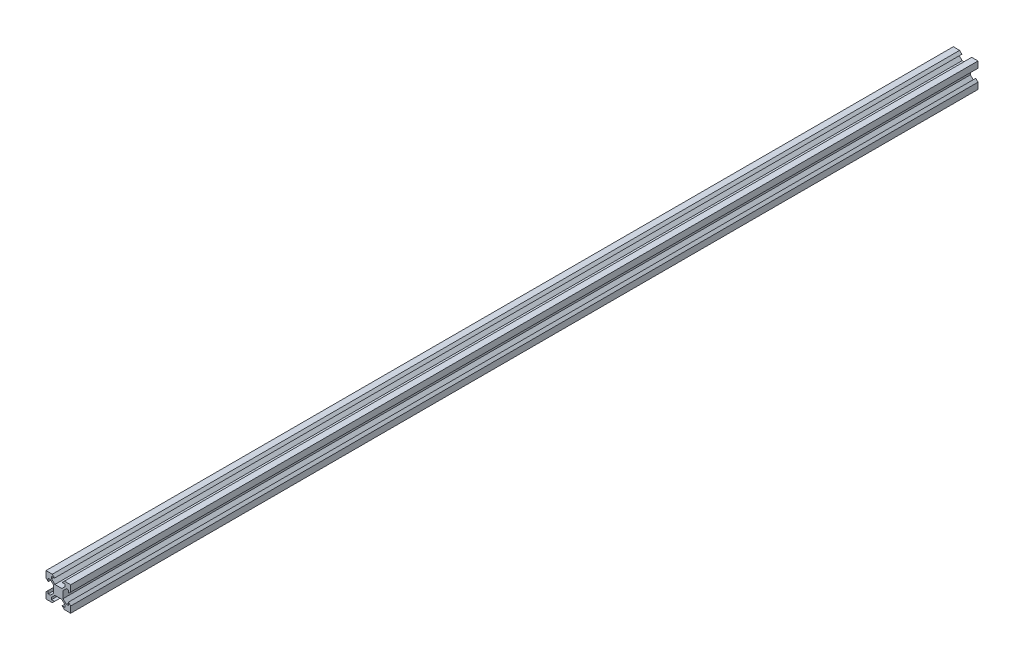
SolidWorks part; units mm, degrees
ref_plane "Front Plane" through (0, 0, 0) normal (0, 0, 1) x (1, 0, 0)
ref_plane "Top Plane" through (0, 0, 0) normal (0, 1, 0) x (1, 0, 0)
ref_plane "Right Plane" through (0, 0, 0) normal (1, 0, 0) x (0, 0, -1)
sketch "Sketch1" plane through (0, 0, 0) normal (0, 0, 1) x (1, 0, 0)
  line L1 (0, 0) -> (20, 0)
  line L2 (0, 0) -> (0, 20)
  line L3 (0, 20) -> (20, 20)
  line L4 (20, 0) -> (20, 20)
  line L5 (0, 0) -> (20, 20) construction
  line L6 (0, 20) -> (20, 0) construction
  point P4 (10, 10)
  dimension "D1" = 20
  dimension "D2" = 20
extrude "Boss-Extrude1" add sketch "Sketch1" along normal blind 735.01
sketch "Sketch2" plane through (0, 0, 735.01) normal (0, 0, 1) x (1, 0, 0)
  line L4 (0, 0) -> (20, 20) construction
  line L5 (4.5, 18.18) -> (6.94, 18.18)
  line L6 (4.5, 16.4758) -> (4.5, 18.18)
  line L15 (7.1658, 13.81) -> (4.5, 16.4758)
  line L17 (12.8342, 13.81) -> (7.1658, 13.81)
  line L27 (15.5, 16.4758) -> (12.8342, 13.81)
  line L29 (15.5, 18.18) -> (15.5, 16.4758)
  line L31 (13.06, 18.18) -> (15.5, 18.18)
  line L33 (14.88, 20) -> (5.12, 20)
  line L35 (6.94, 18.18) -> (5.12, 20)
  line L54 (14.88, 20) -> (13.06, 18.18)
  line L56 (14.88, 0) -> (13.06, 1.82)
  line L57 (6.94, 1.82) -> (5.12, 0)
  line L58 (14.88, 0) -> (5.12, 0)
  line L68 (13.06, 1.82) -> (15.5, 1.82)
  line L71 (15.5, 1.82) -> (15.5, 3.5242)
  line L81 (15.5, 3.5242) -> (12.8342, 6.19)
  line L82 (12.8342, 6.19) -> (7.1658, 6.19)
  line L83 (7.1658, 6.19) -> (4.5, 3.5242)
  line L84 (4.5, 3.5242) -> (4.5, 1.82)
  line L85 (4.5, 1.82) -> (6.94, 1.82)
  line L136 (20, 0) -> (10, 0) construction
  line L137 (0, 0) -> (20, 0) construction
  line L186 (1.82, 4.5) -> (1.82, 6.94)
  line L187 (3.5242, 4.5) -> (1.82, 4.5)
  line L188 (6.19, 7.1658) -> (3.5242, 4.5)
  line L189 (6.19, 12.8342) -> (6.19, 7.1658)
  line L190 (3.5242, 15.5) -> (6.19, 12.8342)
  line L191 (1.82, 15.5) -> (3.5242, 15.5)
  line L192 (1.82, 13.06) -> (1.82, 15.5)
  line L193 (0, 14.88) -> (0, 5.12)
  line L194 (1.82, 6.94) -> (0, 5.12)
  line L195 (0, 14.88) -> (1.82, 13.06)
  line L203 (20, 14.88) -> (18.18, 13.06)
  line L205 (18.18, 6.94) -> (20, 5.12)
  line L206 (20, 14.88) -> (20, 5.12)
  line L207 (18.18, 13.06) -> (18.18, 15.5)
  line L208 (18.18, 15.5) -> (16.4758, 15.5)
  line L209 (16.4758, 15.5) -> (13.81, 12.8342)
  line L210 (13.81, 12.8342) -> (13.81, 7.1658)
  line L211 (13.81, 7.1658) -> (16.4758, 4.5)
  line L212 (16.4758, 4.5) -> (18.18, 4.5)
  line L213 (18.18, 4.5) -> (18.18, 6.94)
extrude "Cut-Extrude1" cut sketch "Sketch2" against normal through all
